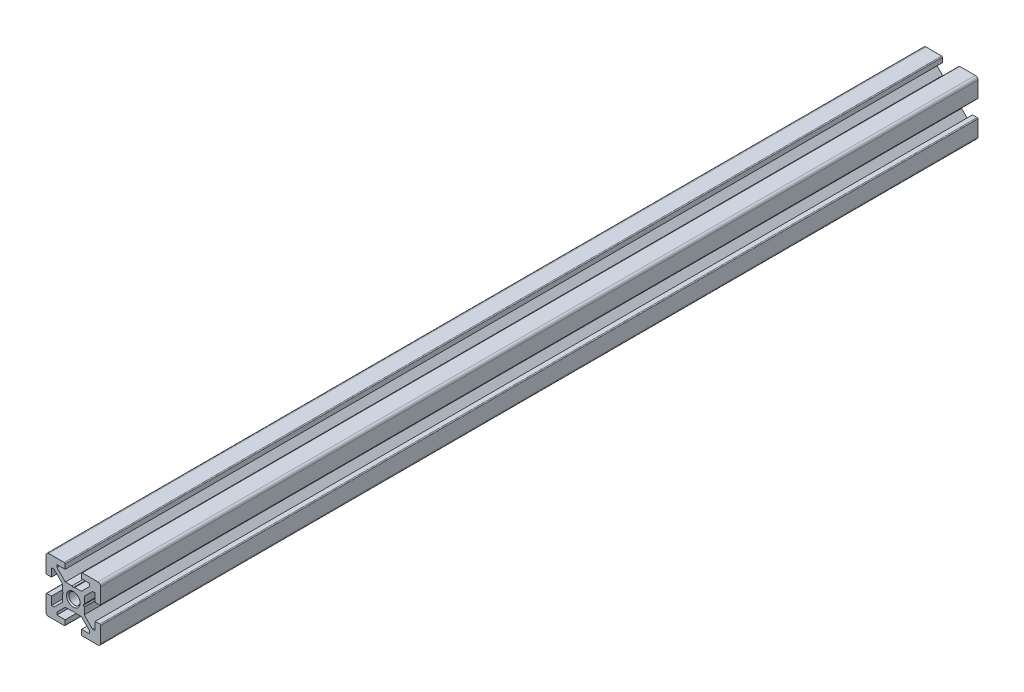
SolidWorks part; units mm, degrees
ref_plane "Front Plane" through (0, 0, 0) normal (0, 0, 1) x (1, 0, 0)
ref_plane "Top Plane" through (0, 0, 0) normal (0, 1, 0) x (1, 0, 0)
ref_plane "Right Plane" through (0, 0, 0) normal (1, 0, 0) x (0, 0, -1)
ref_plane "Plane1" through (0, 0, 0) normal (0, 0, 1) x (1, 0, 0)
sketch "Sketch1" plane through (0, 0, 0) normal (0, 0, 1) x (1, 0, 0)
  line L0 (-10, 9) -> (-10, 3.3)
  line L1 (-9.7, 3) -> (-8, 3)
  line L2 (-8, 3) -> (-8, 6)
  line L3 (-8, 6) -> (-7.0607, 6)
  line L4 (-7.0607, 6) -> (-4, 2.9393)
  line L5 (-4, 2.9393) -> (-4, 0.5196)
  line L6 (-4, 0.5196) -> (-3.7, 0)
  line L7 (-3.7, 0) -> (-4, -0.5196)
  line L8 (-4, -0.5196) -> (-4, -2.9393)
  line L9 (-4, -2.9393) -> (-7.0607, -6)
  line L10 (-7.0607, -6) -> (-8, -6)
  line L11 (-8, -6) -> (-8, -3)
  line L12 (-8, -3) -> (-9.7, -3)
  line L13 (-10, -3.3) -> (-10, -9)
  line L14 (-9, -10) -> (-3.3, -10)
  line L15 (-3, -9.7) -> (-3, -8)
  line L16 (-3, -8) -> (-6, -8)
  line L17 (-6, -8) -> (-6, -7.0607)
  line L18 (-6, -7.0607) -> (-2.9393, -4)
  line L19 (-2.9393, -4) -> (-0.5196, -4)
  line L20 (-0.5196, -4) -> (0, -3.7)
  line L21 (0, -3.7) -> (0.5196, -4)
  line L22 (0.5196, -4) -> (2.9393, -4)
  line L23 (2.9393, -4) -> (6, -7.0607)
  line L24 (6, -7.0607) -> (6, -8)
  line L25 (6, -8) -> (3, -8)
  line L26 (3, -8) -> (3, -9.7)
  line L27 (3.3, -10) -> (9, -10)
  line L28 (10, -9) -> (10, -3.3)
  line L29 (9.7, -3) -> (8, -3)
  line L30 (8, -3) -> (8, -6)
  line L31 (8, -6) -> (7.0606, -6)
  line L32 (7.0606, -6) -> (4, -2.9393)
  line L33 (4, -2.9393) -> (4, -0.5196)
  line L34 (4, -0.5196) -> (3.7, 0)
  line L35 (3.7, 0) -> (4, 0.5196)
  line L36 (4, 0.5196) -> (4, 2.9393)
  line L37 (4, 2.9393) -> (7.0607, 6)
  line L38 (7.0607, 6) -> (8, 6)
  line L39 (8, 6) -> (8, 3)
  line L40 (8, 3) -> (9.7, 3)
  line L41 (10, 3.3) -> (10, 9)
  line L42 (9, 10) -> (3.3, 10)
  line L43 (3, 9.7) -> (3, 8)
  line L44 (3, 8) -> (6, 8)
  line L45 (6, 8) -> (6, 7.0607)
  line L46 (6, 7.0607) -> (2.9393, 4)
  line L47 (2.9393, 4) -> (0.5196, 4)
  line L48 (0.5196, 4) -> (0, 3.7)
  line L49 (0, 3.7) -> (-0.5196, 4)
  line L50 (-0.5196, 4) -> (-2.9394, 4)
  line L51 (-2.9394, 4) -> (-6, 7.0606)
  line L52 (-6, 7.0606) -> (-6, 8)
  line L53 (-6, 8) -> (-3, 8)
  line L54 (-3, 8) -> (-3, 9.7)
  line L55 (-3.3, 10) -> (-9, 10)
  arc A0 (-10, 3.3) -> (-9.7, 3) centre (-9.7, 3.3) ccw
  arc A1 (-9.7, -3) -> (-10, -3.3) centre (-9.7, -3.3) ccw
  arc A2 (-10, -9) -> (-9, -10) centre (-9, -9) ccw
  arc A3 (-3.3, -10) -> (-3, -9.7) centre (-3.3, -9.7) ccw
  arc A4 (3, -9.7) -> (3.3, -10) centre (3.3, -9.7) ccw
  arc A5 (9, -10) -> (10, -9) centre (9, -9) ccw
  arc A6 (10, -3.3) -> (9.7, -3) centre (9.7, -3.3) ccw
  arc A7 (9.7, 3) -> (10, 3.3) centre (9.7, 3.3) ccw
  arc A8 (10, 9) -> (9, 10) centre (9, 9) ccw
  arc A9 (3.3, 10) -> (3, 9.7) centre (3.3, 9.7) ccw
  arc A10 (-3, 9.7) -> (-3.3, 10) centre (-3.3, 9.7) ccw
  arc A11 (-9, 10) -> (-10, 9) centre (-9, 9) ccw
extrude "Boss-Extrude1" add sketch "Sketch1" against normal blind 321
ref_plane "Plane2" through (0, 0, 0) normal (1, 0, 0) x (0, 0, -1)
sketch "Sketch2" plane through (0, 0, 0) normal (1, 0, 0) x (0, 0, -1)
  line L0 (0, 0) -> (0, 2.5)
  line L1 (0, 2.5) -> (0.433, 2.067)
  line L2 (0.433, 2.067) -> (321, 2.067)
  line L3 (321, 2.067) -> (321, 0)
  line L4 (321, 0) -> (0, 0)
  line L5 (321, 0) -> (0, 0) construction
revolve "Cut-Revolve1" cut sketch "Sketch2" angle 360 about L5
cosmetic thread "Cosmetic Thread1" parameters "D1"=15, "D2"=5
cosmetic thread "Cosmetic Thread2" parameters "D1"=15, "D2"=5
ref_plane "Plane3" through (0, 0, 0) normal (1, 0, 0) x (0, 0, -1)
sketch "Sketch3" plane through (0, 0, 0) normal (1, 0, 0) x (0, 0, -1)
  line L0 (0, 0) -> (0, 2.067)
  line L1 (0, 2.067) -> (320.567, 2.067)
  line L2 (320.567, 2.067) -> (321, 2.5)
  line L3 (321, 2.5) -> (321, 0)
  line L4 (321, 0) -> (0, 0)
  line L5 (321, 0) -> (0, 0) construction
revolve "Cut-Revolve2" cut sketch "Sketch3" angle 360 about L5
